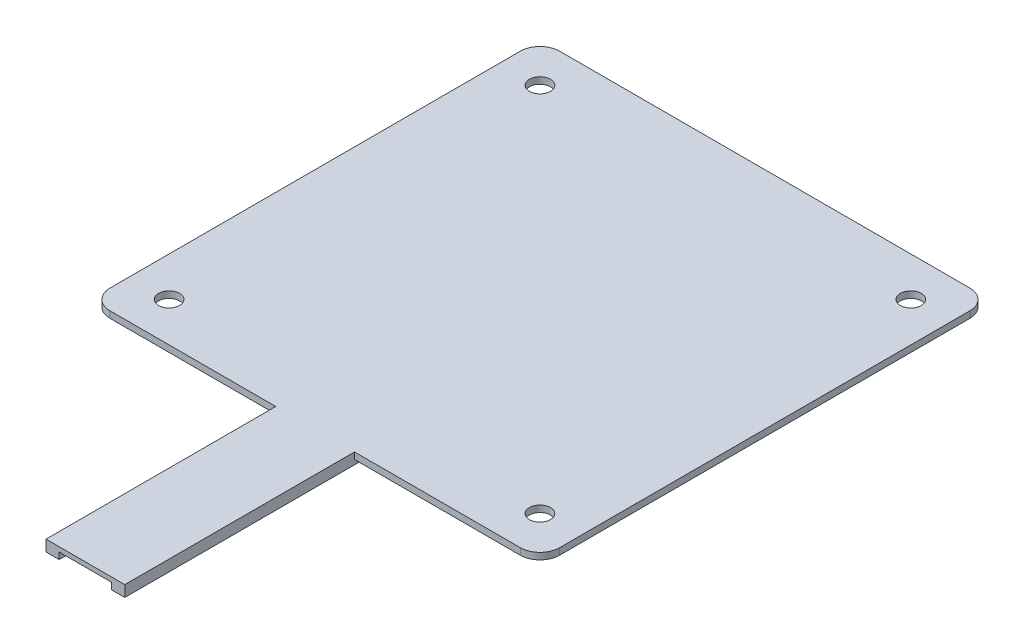
SolidWorks part; units mm, degrees
ref_plane "Front Plane" through (0, 0, 0) normal (0, 0, 1) x (1, 0, 0)
ref_plane "Top Plane" through (0, 0, 0) normal (0, 1, 0) x (1, 0, 0)
ref_plane "Right Plane" through (0, 0, 0) normal (1, 0, 0) x (0, 0, -1)
sketch "Sketch1" plane through (0, 0, 0) normal (0, 1, 0) x (1, 0, 0)
  line L0 (3.5061, 36.1524) -> (3.5061, 22.6037) construction
  line L1 (-18.7439, 22.6037) -> (25.7561, 22.6037)
  line L2 (-18.7439, 22.6037) -> (-18.7439, -21.8963)
  line L3 (-20.7439, 24.6037) -> (27.7561, 24.6037)
  line L4 (25.7561, 22.6037) -> (25.7561, -21.8963)
  line L5 (12.5061, -21.8963) -> (25.7561, -21.8963)
  line L6 (27.7561, 24.6037) -> (27.7561, -23.8963)
  line L7 (-0.4939, -26.8963) -> (-0.4939, -66.8963)
  line L8 (-0.4939, -66.8963) -> (7.5061, -66.8963)
  line L9 (7.5061, -26.8963) -> (7.5061, -66.8963)
  line L10 (-5.4939, -21.8963) -> (-18.7439, -21.8963)
  line L11 (12.5061, -23.8963) -> (27.7561, -23.8963)
  line L12 (9.5061, -26.8963) -> (9.5061, -68.8963)
  line L13 (-2.4939, -68.8963) -> (9.5061, -68.8963)
  line L14 (-2.4939, -26.8963) -> (-2.4939, -68.8963)
  line L15 (-5.4939, -23.8963) -> (-20.7439, -23.8963)
  line L16 (-20.7439, 24.6037) -> (-20.7439, -23.8963)
  arc A0 (7.5061, -26.8963) -> (12.5061, -21.8963) centre (12.5061, -26.8963) cw
  arc A1 (-0.4939, -26.8963) -> (-5.4939, -21.8963) centre (-5.4939, -26.8963) ccw
  arc A2 (9.5061, -26.8963) -> (12.5061, -23.8963) centre (12.5061, -26.8963) cw
  arc A3 (-2.4939, -26.8963) -> (-5.4939, -23.8963) centre (-5.4939, -26.8963) ccw
  dimension "D4" = 5
  dimension "D1" = 44.5
  dimension "D2" = 44.5
  dimension "D3" = 22.25
  dimension "D5" = 4
  dimension "D6" = 2
extrude "Boss-Extrude1" add sketch "Sketch1" along normal blind 0.5
sketch "Sketch2" plane through (0, 0.5, 0) normal (0, 1, 0) x (1, 0, 0)
  line L8 (-20.7439, 24.6037) -> (-20.7439, -23.8963)
  line L9 (-20.7439, -23.8963) -> (-5.4939, -23.8963)
  line L10 (-2.4939, -26.8963) -> (-2.4939, -68.8963)
  line L11 (-2.4939, -68.8963) -> (9.5061, -68.8963)
  line L12 (9.5061, -68.8963) -> (9.5061, -26.8963)
  line L13 (12.5061, -23.8963) -> (27.7561, -23.8963)
  line L14 (27.7561, -23.8963) -> (27.7561, 24.6037)
  line L15 (27.7561, 24.6037) -> (-20.7439, 24.6037)
  line L16 (-20.7439, 24.6037) -> (-20.7439, -23.8963)
  line L17 (-20.7439, -23.8963) -> (-5.4939, -23.8963)
  line L18 (-2.4939, -26.8963) -> (-2.4939, -68.8963)
  line L19 (-2.4939, -68.8963) -> (9.5061, -68.8963)
  line L20 (9.5061, -68.8963) -> (9.5061, -26.8963)
  line L21 (12.5061, -23.8963) -> (27.7561, -23.8963)
  line L22 (27.7561, -23.8963) -> (27.7561, 24.6037)
  line L23 (27.7561, 24.6037) -> (-20.7439, 24.6037)
  arc A2 (-2.4939, -26.8963) -> (-5.4939, -23.8963) centre (-5.4939, -26.8963) ccw
  arc A3 (12.5061, -23.8963) -> (9.5061, -26.8963) centre (12.5061, -26.8963) ccw
  arc A4 (-2.4939, -26.8963) -> (-5.4939, -23.8963) centre (-5.4939, -26.8963) ccw
  arc A5 (12.5061, -23.8963) -> (9.5061, -26.8963) centre (12.5061, -26.8963) ccw
  dimension "D1" = 0
extrude "Boss-Extrude2" add sketch "Sketch2" along normal blind 1.2
sketch "Sketch3" plane through (0, 0, 0) normal (0, -1, 0) x (1, 0, 0)
  line L0 (-2.4939, 68.8963) -> (9.5061, 68.8963) construction
  line L1 (-0.4939, 66.8963) -> (7.5061, 66.8963)
  line L2 (-0.4939, 66.8963) -> (-0.4939, 68.8963)
  line L3 (-0.4939, 68.8963) -> (7.5061, 68.8963)
  line L4 (7.5061, 66.8963) -> (7.5061, 68.8963)
extrude "Cut-Extrude1" cut sketch "Sketch3" against normal blind 1
sketch "Sketch4" plane through (0, 1.7, 0) normal (0, 1, 0) x (1, 0, 0)
  line L8 (-12.4939, -33.8963) -> (19.5061, -33.8963)
  line L16 (37.7561, 34.6037) -> (-30.7439, 34.6037)
  line L17 (-30.7439, 34.6037) -> (-30.7439, -33.8963)
  line L18 (-30.7439, -33.8963) -> (-12.4939, -33.8963)
  line L19 (-12.4939, -33.8963) -> (-12.4939, -78.8963)
  line L20 (-12.4939, -78.8963) -> (19.5061, -78.8963)
  line L21 (19.5061, -78.8963) -> (19.5061, -33.8963)
  line L22 (19.5061, -33.8963) -> (37.7561, -33.8963)
  line L23 (37.7561, -33.8963) -> (37.7561, 34.6037)
  line L24 (37.7561, 34.6037) -> (-30.7439, 34.6037)
  line L25 (-30.7439, 34.6037) -> (-30.7439, -33.8963)
  line L26 (-30.7439, -33.8963) -> (-12.4939, -33.8963)
  line L30 (19.5061, -33.8963) -> (37.7561, -33.8963)
  line L31 (37.7561, -33.8963) -> (37.7561, 34.6037)
  dimension "D1" = 10
extrude "Boss-Extrude3" add sketch "Sketch4" against normal blind 1
fillet "Fillet1" radius 3 4 edges at (-30.7439, 1.2, 33.8963) (37.7561, 1.2, 33.8963) (37.7561, 1.2, -34.6037) (-30.7439, 1.2, -34.6037)
sketch "Sketch5" plane through (0, 0.7, 0) normal (0, -1, 0) x (1, 0, 0)
  line L0 (-27.7439, 33.8963) -> (-2.4939, 33.8963) construction
  line L1 (-30.7439, -31.6037) -> (-30.7439, 30.8963) construction
  line L2 (37.7561, 30.8963) -> (37.7561, -31.6037) construction
  line L3 (9.5061, 33.8963) -> (34.7561, 33.8963) construction
  line L4 (34.7561, -34.6037) -> (-27.7439, -34.6037) construction
  circle A0 centre (-24.7439, 27.8963) radius 1.6
  circle A1 centre (31.7561, 27.8963) radius 1.6
  circle A2 centre (31.7561, -28.6037) radius 1.6
  circle A3 centre (-24.7439, -28.6037) radius 1.6
  dimension "D1" = 3.2
  dimension "D2" = 6
  dimension "D4" = 6
  dimension "D5" = 6
  dimension "D6" = 6
  dimension "D7" = 6
  dimension "D8" = 6
  dimension "D9" = 6
  dimension "D3" = 6
extrude "Cut-Extrude2" cut sketch "Sketch5" against normal blind 1
